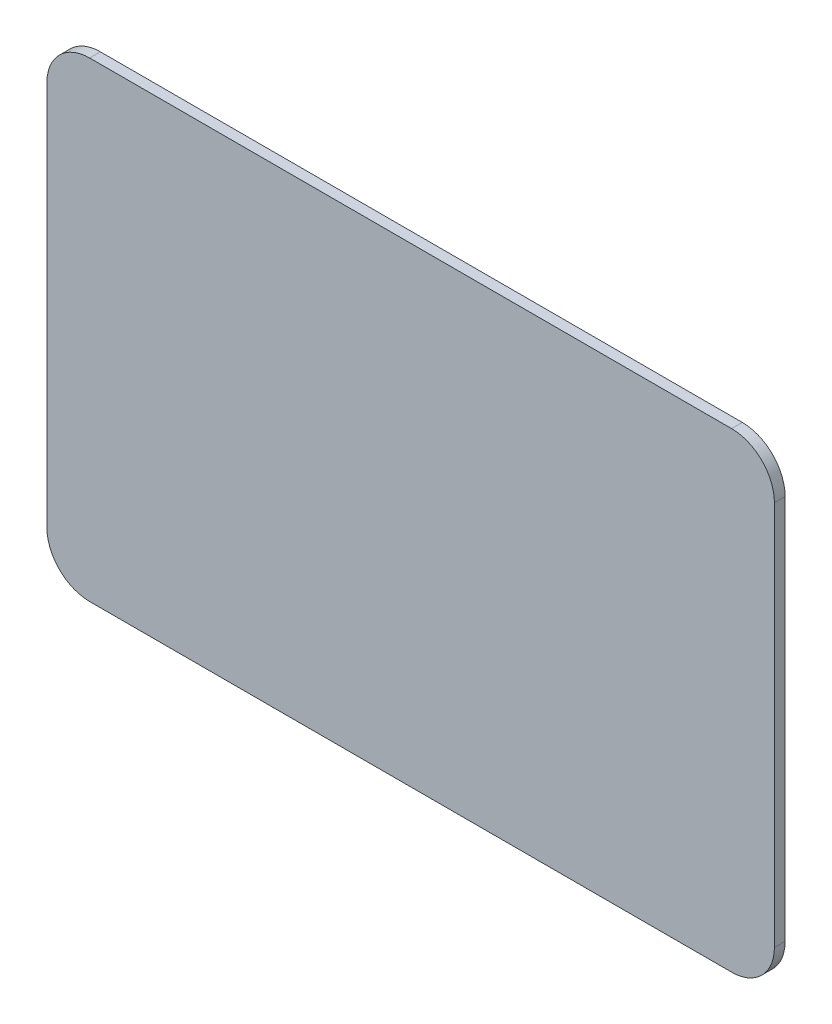
SolidWorks part; units mm, degrees
material "Acrylic (Medium-high impact)"
ref_plane "X-Y Datum" through (0, 0, 0) normal (0, 0, 1) x (1, 0, 0)
ref_plane "X-Z Datum" through (0, 0, 0) normal (0, 1, 0) x (1, 0, 0)
ref_plane "Y-Z Datum" through (0, 0, 0) normal (1, 0, 0) x (0, 0, -1)
sketch "Sketch1" plane through (0, 0, 0) normal (0, 0, 1) x (1, 0, 0)
  line L1 (-53.975, 34.925) -> (53.975, 34.925)
  line L2 (-53.975, 34.925) -> (-53.975, -34.925)
  line L3 (-53.975, -34.925) -> (53.975, -34.925)
  line L4 (53.975, 34.925) -> (53.975, -34.925)
  line L5 (-53.975, 34.925) -> (53.975, -34.925) construction
  line L6 (-53.975, -34.925) -> (53.975, 34.925) construction
  point P0 (0, 0)
  dimension "D1" = 107.95
  dimension "D2" = 69.85
extrude "Boss-Extrude1" add sketch "Sketch1" along normal blind 1.5875
fillet "Fillet1" radius 6.35 4 edges at (53.975, -34.925, 0.7937) (53.975, 34.925, 0.7937) (-53.975, 34.925, 0.7937) (-53.975, -34.925, 0.7937)
